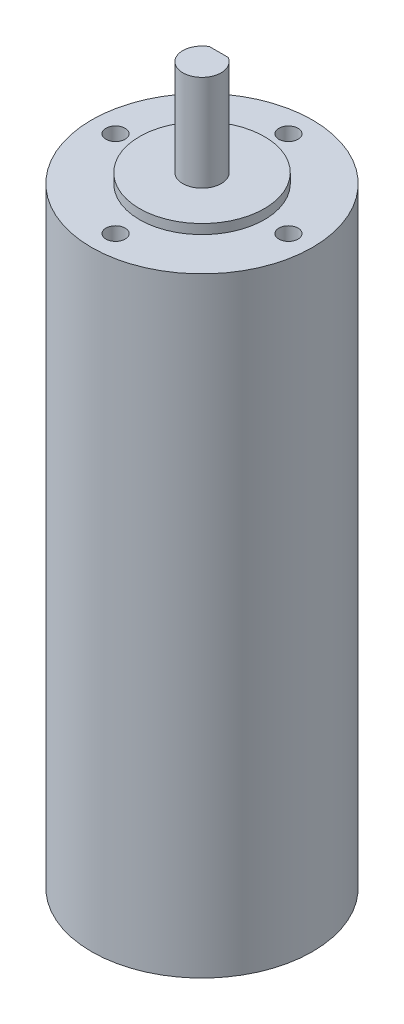
SolidWorks part; units mm, degrees
ref_plane "Front Plane" through (0, 0, 0) normal (0, 0, 1) x (1, 0, 0)
ref_plane "Top Plane" through (0, 0, 0) normal (0, 1, 0) x (1, 0, 0)
ref_plane "Right Plane" through (0, 0, 0) normal (1, 0, 0) x (0, 0, -1)
sketch "Sketch2" plane through (0, 0, 0) normal (0, 1, 0) x (1, 0, 0)
  circle A0 centre (0, 0) radius 23
  dimension "D1" = 46
extrude "Boss-Extrude1" add sketch "Sketch2" along normal blind 127
sketch "Sketch3" plane through (0, 127, 0) normal (0, 1, 0) x (1, 0, 0)
  circle A0 centre (0, 0) radius 13
  dimension "D1" = 26
extrude "Boss-Extrude2" add sketch "Sketch3" along normal blind 2
sketch "Sketch4" plane through (0, 129, 0) normal (0, 1, 0) x (1, 0, 0)
  circle A0 centre (0, 0) radius 4
  dimension "D1" = 8
extrude "Boss-Extrude3" add sketch "Sketch4" along normal blind 20
sketch "Sketch8" plane through (0, 127, 0) normal (0, 1, 0) x (1, 0, 0)
  circle A0 centre (0, 18) radius 2
  circle A1 centre (18, 0) radius 2
  circle A2 centre (0, -18) radius 2
  circle A3 centre (-18, 0) radius 2
  point P11 (0, 0)
  dimension "D1" = 4
  dimension "D3" = 18
  dimension "D2" = 4
extrude "Cut-Extrude1" cut sketch "Sketch8" against normal blind 10
sketch "Sketch10" plane through (0, 149, 0) normal (0, 1, 0) x (1, 0, 0)
  line L0 (-1.9365, 3.5) -> (1.9365, 3.5)
  circle A0 centre (0, 0) radius 4 construction
  circle A1 centre (0, 0) radius 4
  point P5 (0, 3.5)
  circle M2 centre (0, 0) radius 4
  dimension "D3" = 8
  dimension "D1" = 3.5
  dimension "D2" = 0
extrude "Cut-Extrude2" cut sketch "Sketch10" against normal blind 12 contours L0 M2
